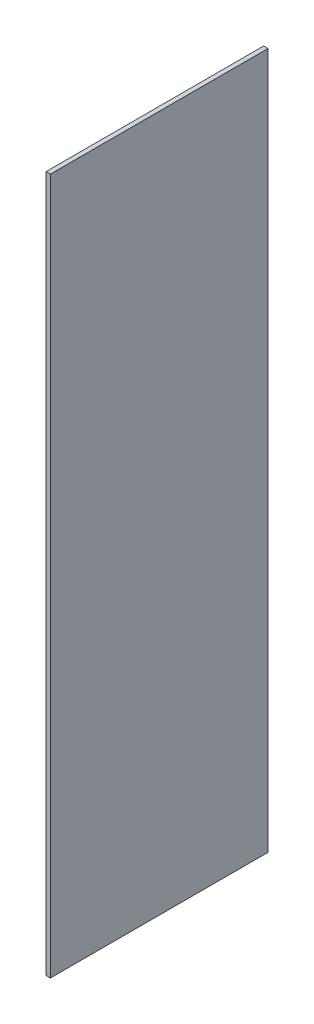
SolidWorks part; units mm, degrees
ref_plane "Front Plane" through (0, 0, 0) normal (0, 0, 1) x (1, 0, 0)
ref_plane "Top Plane" through (0, 0, 0) normal (0, 1, 0) x (1, 0, 0)
ref_plane "Right Plane" through (0, 0, 0) normal (1, 0, 0) x (0, 0, -1)
sketch "Sketch1" plane through (0, 0, 0) normal (0, 0, 1) x (1, 0, 0)
  line L1 (0, 0) -> (0.1, 0)
  line L2 (0, 0) -> (0, 16)
  line L3 (0, 16) -> (0.1, 16)
  line L4 (0.1, 0) -> (0.1, 16)
  dimension "D2" = 0.1
extrude "Boss-Extrude1" add sketch "Sketch1" along normal blind 5
equation "\"A.L\"= 0.07m"
equation "\"A.h\"= 0.007m"
equation "\"A.d\"= 0.005m"
equation "\"A.delta\"= 45.0001"
equation "\"A.w\"= 0m"
equation "\"A.v\"= 0.013m"
equation "\"A.s\"= 0.014m"
equation "\"A.t\"= 0.007m"
equation "\"B.L\"= 0.065m"
equation "\"B.h\"= 0.008m"
equation "\"B.s\"= 0.016m"
equation "\"B.t\"= 0.008m"
equation "\"C.h\"= 0.0065m"
equation "\"C.d\"= 0.005m"
equation "\"C.L\"= 0.05m"
equation "\"C.wmax\"= 0.003m"
equation "\"D.L\"= 0.06m"
equation "\"D.h\"= 0.008m"
equation "\"D.s\"= 0.012m"
equation "\"D.t\"= 0.008m"
equation "\"a_h\"= 0.0001m"
equation "\"a_d\"= 0.005m"
equation "\"a_L\"= 0.008m"
equation "\"b_h\"= 0.0004m"
equation "\"b_d\"= 0.005m"
equation "\"b_L\"= 0.008m"
equation "\"c_h\"= 0.0001m"
equation "\"c_d\"= 0.005m"
equation "\"c_L\"= 0.01m"
equation "\"d_h\"= 0.0001m"
equation "\"d_d\"= 0.005m"
equation "\"d_L\"= 0.01m"
equation "\"S.h\"= 0.015m"
equation "\"S.L\"= 0.09175m"
equation "\"D1@Sketch1\"=\"c_L\"+0.006"
equation "\"D2@Sketch1\"=\"c_h\""
equation "\"D1@Boss-Extrude1\"=0.005m"
